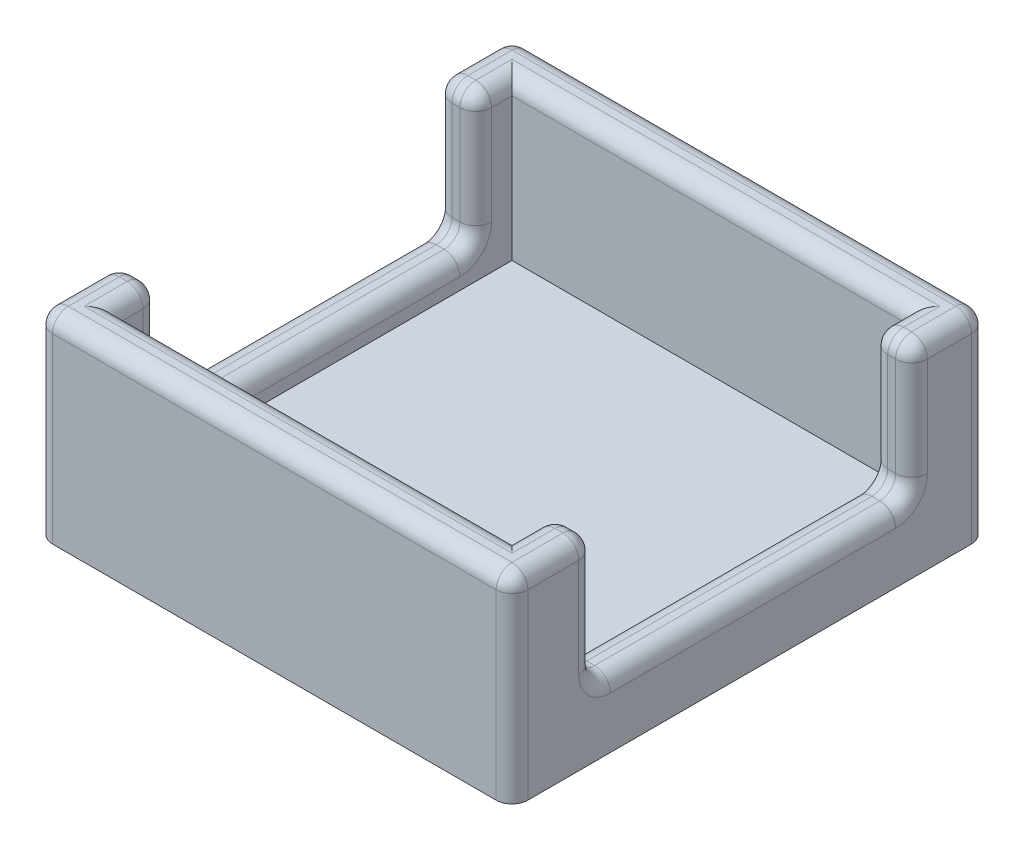
SolidWorks part; units mm, degrees
ref_plane "Front Plane" through (0, 0, 0) normal (0, 0, 1) x (1, 0, 0)
ref_plane "Top Plane" through (0, 0, 0) normal (0, 1, 0) x (1, 0, 0)
ref_plane "Right Plane" through (0, 0, 0) normal (1, 0, 0) x (0, 0, -1)
sketch "Sketch5" plane through (0, 0, 0) normal (0, 1, 0) x (1, 0, 0)
  line L1 (-30, -30) -> (30, -30)
  line L2 (-30, -30) -> (-30, 30)
  line L3 (-30, 30) -> (30, 30)
  line L4 (30, -30) -> (30, 30)
  line L5 (-30, -30) -> (30, 30) construction
  line L6 (-30, 30) -> (30, -30) construction
  point P0 (0, 0)
  dimension "D1" = 60
  dimension "D2" = 60
extrude "Boss-Extrude3" add sketch "Sketch5" along normal blind 25
shell "Shell1" thickness 5
sketch "Sketch6" plane through (30, 0, 0) normal (1, 0, 0) x (0, 0, -1)
  line L3 (-19.5771, 58.505) -> (20.4229, 58.505)
  line L4 (-19.5771, 58.505) -> (-19.5771, 8.505)
  line L5 (-19.5771, 8.505) -> (20.4229, 8.505)
  line L6 (20.4229, 58.505) -> (20.4229, 8.505)
  line L7 (-19.5771, 58.505) -> (20.4229, 8.505) construction
  line L8 (-19.5771, 8.505) -> (20.4229, 58.505) construction
  dimension "D1" = 50
  dimension "D2" = 40
extrude "Cut-Extrude2" cut sketch "Sketch6" against normal blind 100
fillet "Fillet2" radius 2 36 edges at (25, 16.7525, -20.4229) (30, 16.7525, -20.4229) (30, 16.7525, 19.5771) (25, 16.7525, 19.5771) (-30, 16.7525, 19.5771) (-30, 16.7525, -20.4229) (-25, 16.7525, -20.4229) (-25, 16.7525, 19.5771) (27.5, 8.505, -20.4229) (30, 8.505, -0.4229) (27.5, 8.505, 19.5771) (25, 8.505, -0.4229) (-30, 8.505, -0.4229) (-27.5, 8.505, -20.4229) (-25, 8.505, -0.4229) (-27.5, 8.505, 19.5771) (0, 25, 30) (-30, 25, 24.7885) (-27.5, 25, 19.5771) (-25, 25, 22.2885) (0, 25, 25) (25, 25, 22.2885) (27.5, 25, 19.5771) (30, 25, 24.7885) (0, 25, -30) (30, 25, -25.2115) (27.5, 25, -20.4229) (25, 25, -22.7115) (0, 25, -25) (-25, 25, -22.7115) (-27.5, 25, -20.4229) (-30, 25, -25.2115) (30, 12.5, -30) (-30, 12.5, -30) (30, 12.5, 30) (-30, 12.5, 30)
